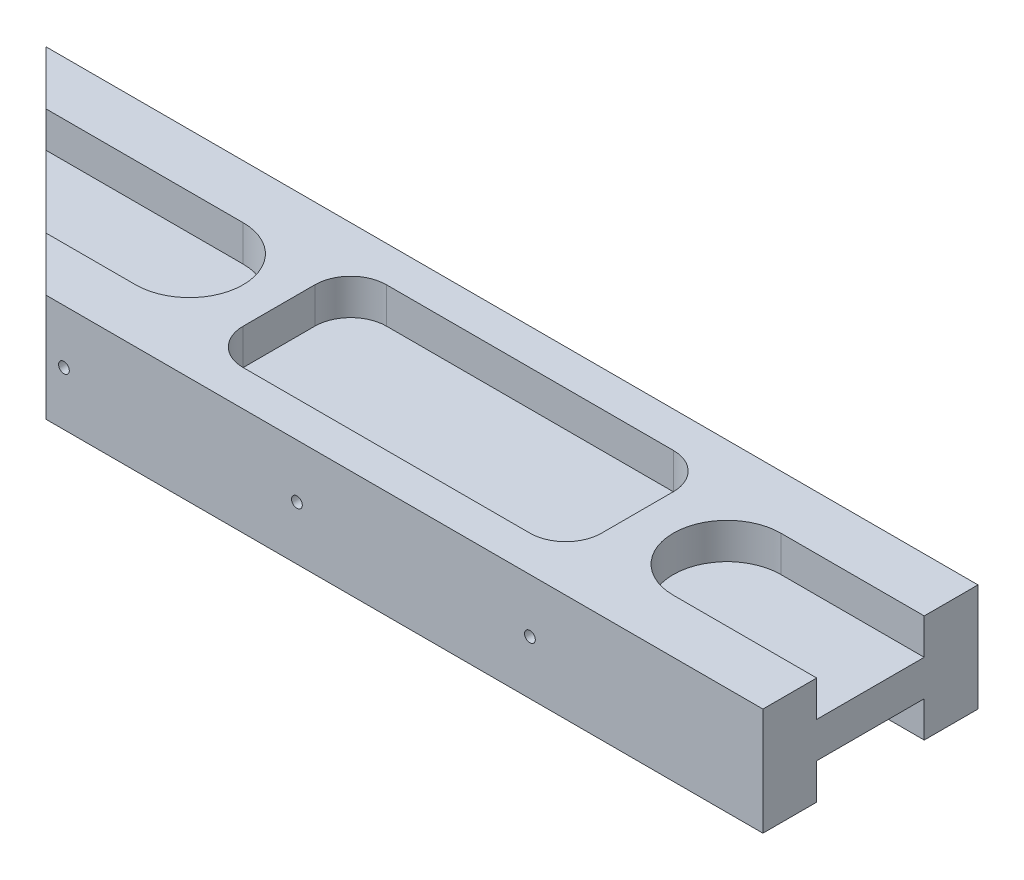
SolidWorks part; units mm, degrees
ref_plane "Front Plane" through (0, 0, 0) normal (0, 0, 1) x (1, 0, 0)
ref_plane "Top Plane" through (0, 0, 0) normal (0, 1, 0) x (1, 0, 0)
ref_plane "Right Plane" through (0, 0, 0) normal (1, 0, 0) x (0, 0, -1)
sketch "Sketch1" plane through (0, 0, 0) normal (0, 1, 0) x (1, 0, 0)
  line L0 (0, 0) -> (-100, 0)
  line L1 (-100, 0) -> (-130, 30)
  line L2 (-130, 30) -> (0, 30)
  line L3 (0, 30) -> (0, 0)
  dimension "D1" = 100
  dimension "D2" = 130
  dimension "D3" = 30
extrude "Boss-Extrude1" add sketch "Sketch1" along normal blind 15
sketch "Sketch2" plane through (0, 15, 0) normal (0, 1, 0) x (1, 0, 0)
  line L0 (-135, 15) -> (-95, 15) construction
  line L1 (-135, 22.5) -> (-95, 22.5)
  line L2 (-135, 7.5) -> (-95, 7.5)
  line L3 (-130, 30) -> (-100, 0) construction
  line L4 (-115, 15) -> (0, 15) construction
  line L5 (0, 0) -> (0, 30) construction
  line L6 (-57.5, 15) -> (-57.5, 30) construction
  line L7 (0, 30) -> (-130, 30) construction
  line L8 (20, 15) -> (-20, 15) construction
  line L9 (20, 22.5) -> (-20, 22.5)
  line L10 (20, 7.5) -> (-20, 7.5)
  arc A0 (-135, 22.5) -> (-135, 7.5) centre (-135, 15) ccw
  arc A1 (-95, 7.5) -> (-95, 22.5) centre (-95, 15) ccw
  arc A2 (20, 22.5) -> (20, 7.5) centre (20, 15) cw
  arc A3 (-20, 7.5) -> (-20, 22.5) centre (-20, 15) cw
  point P2 (-115, 15)
  point P9 (-115, 15)
  point P20 (0, 15)
  dimension "D1" = 40
  dimension "D2" = 15
extrude "Cut-Extrude1" cut sketch "Sketch2" against normal blind 5
sketch "Sketch3" plane through (0, 0, 0) normal (0, -1, 0) x (1, 0, 0)
  line L0 (0, 0) -> (0, -30) construction
  line L1 (-20, -7.5) -> (0, -7.5) construction
  line L2 (0, -22.5) -> (-20, -22.5) construction
  line L3 (-130, -30) -> (-100, 0) construction
  line L4 (-95, -22.5) -> (-122.5, -22.5) construction
  line L5 (-107.5, -7.5) -> (-95, -7.5) construction
  line L6 (0, -7.5) -> (0, -22.5)
  line L7 (-20, -7.5) -> (0, -7.5)
  line L8 (0, -22.5) -> (-20, -22.5)
  line L9 (-122.5, -22.5) -> (-107.5, -7.5)
  line L10 (-95, -22.5) -> (-122.5, -22.5)
  line L11 (-107.5, -7.5) -> (-95, -7.5)
  arc A0 (-20, -7.5) -> (-20, -22.5) centre (-20, -15) ccw construction
  arc A1 (-95, -22.5) -> (-95, -7.5) centre (-95, -15) ccw construction
  arc A2 (-20, -7.5) -> (-20, -22.5) centre (-20, -15) ccw
  arc A3 (-95, -22.5) -> (-95, -7.5) centre (-95, -15) ccw
extrude "Cut-Extrude2" cut sketch "Sketch3" against normal blind 5
sketch "Sketch4" plane through (0, 0, -30) normal (0, 0, -1) x (-1, 0, 0)
  line L0 (0, 7.5) -> (130, 7.5) construction
  line L1 (0, 15) -> (0, 0) construction
  line L2 (130, 15) -> (130, 0) construction
  circle A0 centre (65, 7.5) radius 0.75
  circle A1 centre (32.5, 7.5) radius 0.75
  circle A2 centre (97.5, 7.5) radius 0.75
  dimension "D1" = 1.5
  dimension "D2" = 32.5
  dimension "D3" = 32.5
extrude "Cut-Extrude3" cut sketch "Sketch4" against normal up to surface (30 mm away) up to face at (-50, 7.5, 0)
sketch "Sketch5" plane through (0, 15, 0) normal (0, 1, 0) x (1, 0, 0)
  line L0 (-100, 0) -> (0, 0) construction
  line L1 (-77.5, 25) -> (-37.5, 25)
  line L2 (-82.5, 20) -> (-82.5, 10)
  line L3 (-77.5, 5) -> (-37.5, 5)
  line L4 (-32.5, 20) -> (-32.5, 10)
  line L5 (0, 30) -> (-130, 30) construction
  arc A0 (-95, 7.5) -> (-95, 22.5) centre (-95, 15) ccw construction
  arc A1 (-20, 22.5) -> (-20, 7.5) centre (-20, 15) ccw construction
  arc A2 (-37.5, 25) -> (-32.5, 20) centre (-37.5, 20) cw
  arc A3 (-37.5, 5) -> (-32.5, 10) centre (-37.5, 10) ccw
  arc A4 (-82.5, 10) -> (-77.5, 5) centre (-77.5, 10) ccw
  arc A5 (-77.5, 25) -> (-82.5, 20) centre (-77.5, 20) ccw
  point P4 (-87.5, 15)
  point P5 (-27.5, 15)
  dimension "D5" = 5
  dimension "D1" = 5
  dimension "D2" = 5
  dimension "D3" = 5
  dimension "D4" = 5
extrude "Cut-Extrude4" cut sketch "Sketch5" against normal blind 5
